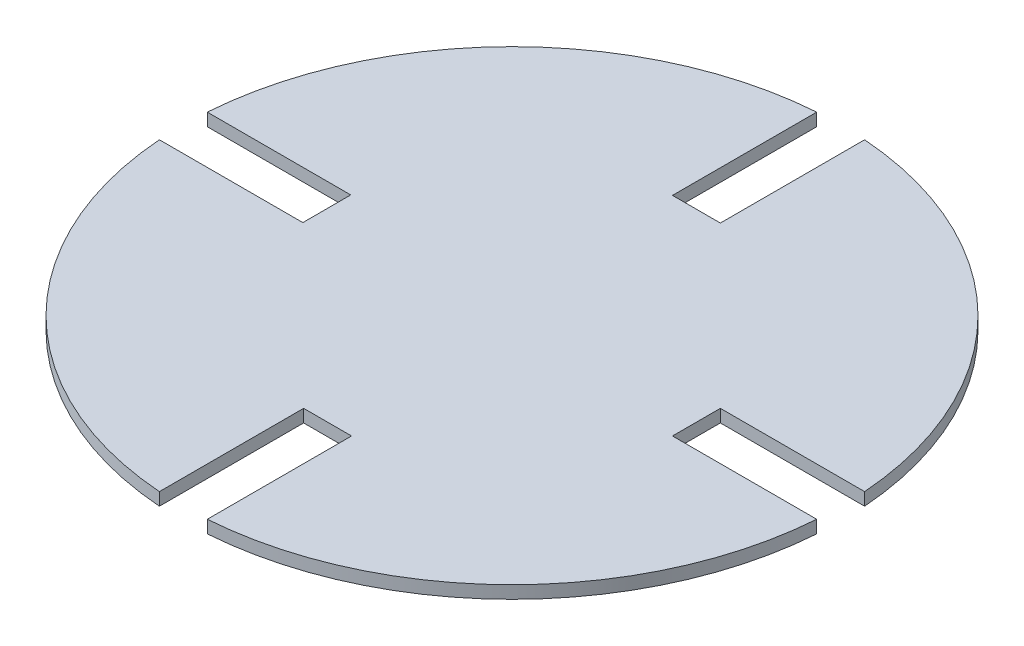
SolidWorks part; units mm, degrees
ref_plane "Front Plane" through (0, 0, 0) normal (0, 0, 1) x (1, 0, 0)
ref_plane "Top Plane" through (0, 0, 0) normal (0, 1, 0) x (1, 0, 0)
ref_plane "Right Plane" through (0, 0, 0) normal (1, 0, 0) x (0, 0, -1)
sketch "Sketch1" plane through (0, 0, 0) normal (0, 1, 0) x (1, 0, 0)
  circle A0 centre (0, 0) radius 82.55
extrude "Boss-Extrude1" add sketch "Sketch1" along normal blind 3.175
sketch "Sketch2" plane through (0, 3.175, 0) normal (0, 1, 0) x (1, 0, 0)
  line L5 (-105.9993, -6) -> (-46.4007, -6)
  line L6 (-105.9993, -6) -> (-105.9993, 6)
  line L7 (-105.9993, 6) -> (-46.4007, 6)
  line L8 (-46.4007, -6) -> (-46.4007, 6)
  line L9 (-105.9993, -6) -> (-46.4007, 6) construction
  line L10 (-105.9993, 6) -> (-46.4007, -6) construction
  line L11 (106.1999, -6) -> (46.2001, -6)
  line L12 (106.1999, -6) -> (106.1999, 6)
  line L13 (106.1999, 6) -> (46.2001, 6)
  line L14 (46.2001, -6) -> (46.2001, 6)
  line L15 (106.1999, -6) -> (46.2001, 6) construction
  line L16 (106.1999, 6) -> (46.2001, -6) construction
  line L23 (6, 46.2001) -> (-6, 46.2001)
  line L24 (6, 46.2001) -> (6, 106.1999)
  line L25 (6, 106.1999) -> (-6, 106.1999)
  line L26 (-6, 46.2001) -> (-6, 106.1999)
  line L27 (6, 46.2001) -> (-6, 106.1999) construction
  line L28 (6, 106.1999) -> (-6, 46.2001) construction
  line L29 (6, -106.1999) -> (-6, -106.1999)
  line L30 (6, -106.1999) -> (6, -46.2001)
  line L31 (6, -46.2001) -> (-6, -46.2001)
  line L32 (-6, -106.1999) -> (-6, -46.2001)
  line L33 (6, -106.1999) -> (-6, -46.2001) construction
  line L34 (6, -46.2001) -> (-6, -106.1999) construction
  point P18 (0, 0)
  dimension "D1" = 59.9999
  dimension "D2" = 12
  dimension "D3" = 12
  dimension "D4" = 59.9999
extrude "Cut-Extrude1" cut sketch "Sketch2" against normal blind 3.175
